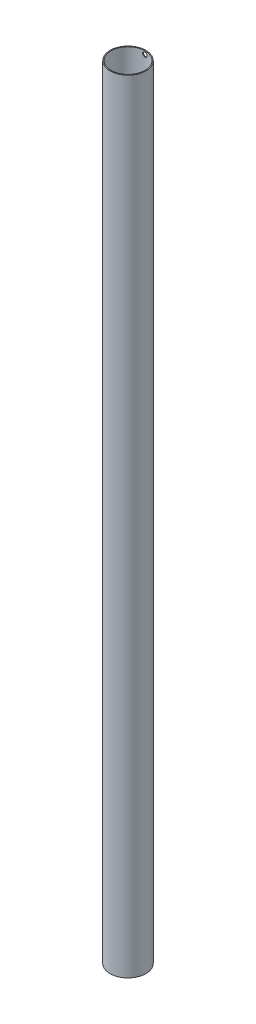
SolidWorks part; units mm, degrees
ref_plane "Plan de face" through (0, 0, 0) normal (0, 0, 1) x (1, 0, 0)
ref_plane "Plan de dessus" through (0, 0, 0) normal (0, 1, 0) x (1, 0, 0)
ref_plane "Plan de droite" through (0, 0, 0) normal (1, 0, 0) x (0, 0, -1)
sketch "Esquisse1" plane through (0, 0, 0) normal (0, 1, 0) x (1, 0, 0)
  circle A0 centre (0, 0) radius 40
  circle A1 centre (0, 0) radius 38
  dimension "D1" = 2
extrude "Boss.-Extru.1" add sketch "Esquisse1" along normal blind 1750
sketch "Esquisse2" plane through (0, 0, 0) normal (0, -1, 0) x (1, 0, 0)
  line L0 (40, 0) -> (-40, 0) construction
  line L1 (0, -40) -> (0, 40) construction
  circle A0 centre (0, 0) radius 40 construction
sketch "Esquisse3" plane through (0, 1750, 0) normal (0, 1, 0) x (1, 0, 0)
  line L0 (0, -40) -> (0, 40) construction
  line L1 (40, 0) -> (-40, 0) construction
  circle A0 centre (0, 0) radius 40 construction
sketch "Esquisse5" plane through (0, 0, 0) normal (0, 0, 1) x (1, 0, 0)
  line L0 (40, 1750) -> (-40, 1750) construction
  circle A0 centre (0, 1742.5) radius 5
  dimension "D1" = 7.5
extrude "Enlèv. mat.-Extru.1" cut sketch "Esquisse5" against normal through all
